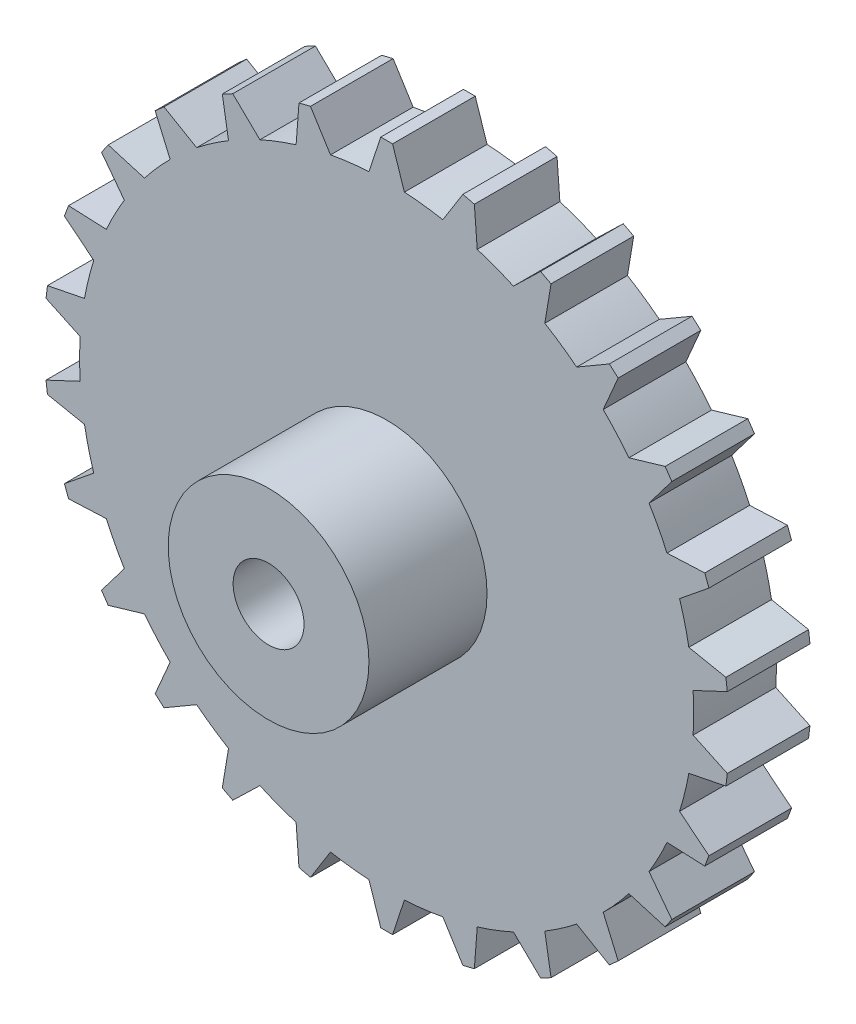
SolidWorks part; units mm, degrees
ref_plane "Front Plane" through (0, 0, 0) normal (0, 0, 1) x (1, 0, 0)
ref_plane "Top Plane" through (0, 0, 0) normal (0, 1, 0) x (1, 0, 0)
ref_plane "Right Plane" through (0, 0, 0) normal (1, 0, 0) x (0, 0, -1)
sketch "Sketch1" plane through (0, 0, 0) normal (0, 0, 1) x (1, 0, 0)
  line L0 (0, 0) -> (0, 21.7596) construction
  line L17 (6.4537, 28.2728) -> (4.7554, 25.5614)
  line L18 (6.4537, 28.2728) -> (7.4246, 28.0335)
  line L19 (7.4246, 28.0335) -> (7.6683, 24.8435)
  line L20 (13.0322, 25.9068) -> (10.7345, 23.6806)
  line L21 (13.0322, 25.9068) -> (13.9177, 25.442)
  line L22 (13.9177, 25.442) -> (13.3909, 22.2864)
  line L23 (18.8534, 22.0351) -> (16.0897, 20.4235)
  line L24 (18.8534, 22.0351) -> (19.602, 21.372)
  line L25 (19.602, 21.372) -> (18.3352, 18.4342)
  line L26 (23.579, 16.8829) -> (20.5098, 15.9796)
  line L27 (-1.5, 25.9567) -> (1.5, 25.9567) construction
  line L28 (-0.5, 28.9957) -> (0.5, 28.9957)
  line L29 (-0.5, 28.9957) -> (-1.5, 25.9567)
  line L30 (0.5, 28.9957) -> (1.5, 25.9567)
  line L31 (23.579, 16.8829) -> (24.147, 16.0599)
  line L32 (24.147, 16.0599) -> (22.214, 13.5106)
  line L33 (26.9341, 10.7495) -> (23.738, 10.6069)
  line L34 (26.9341, 10.7495) -> (27.2887, 9.8145)
  line L35 (27.2887, 9.8145) -> (24.8018, 7.8018)
  line L36 (28.724, 3.9914) -> (25.5866, 4.6178)
  line L37 (28.724, 3.9914) -> (28.8445, 2.9987)
  line L38 (28.8445, 2.9987) -> (25.9482, 1.6397)
  line L39 (28.8445, -2.9987) -> (25.9482, -1.6397)
  line L40 (28.8445, -2.9987) -> (28.724, -3.9914)
  line L41 (28.724, -3.9914) -> (25.5866, -4.6178)
  line L42 (27.2887, -9.8145) -> (24.8018, -7.8018)
  line L43 (27.2887, -9.8145) -> (26.9341, -10.7495)
  line L44 (26.9341, -10.7495) -> (23.738, -10.6069)
  line L45 (24.147, -16.0599) -> (22.214, -13.5106)
  line L46 (24.147, -16.0599) -> (23.579, -16.8829)
  line L47 (23.579, -16.8829) -> (20.5098, -15.9796)
  line L48 (19.602, -21.372) -> (18.3352, -18.4342)
  line L49 (19.602, -21.372) -> (18.8534, -22.0351)
  line L50 (18.8534, -22.0351) -> (16.0897, -20.4235)
  line L51 (13.9177, -25.442) -> (13.3909, -22.2864)
  line L52 (13.9177, -25.442) -> (13.0322, -25.9068)
  line L53 (13.0322, -25.9068) -> (10.7345, -23.6806)
  line L54 (7.4246, -28.0335) -> (7.6683, -24.8435)
  line L55 (7.4246, -28.0335) -> (6.4537, -28.2728)
  line L56 (6.4537, -28.2728) -> (4.7554, -25.5614)
  line L57 (0.5, -28.9957) -> (1.5, -25.9567)
  line L58 (0.5, -28.9957) -> (-0.5, -28.9957)
  line L59 (-0.5, -28.9957) -> (-1.5, -25.9567)
  line L60 (-6.4537, -28.2728) -> (-4.7554, -25.5614)
  line L61 (-6.4537, -28.2728) -> (-7.4246, -28.0335)
  line L62 (-7.4246, -28.0335) -> (-7.6683, -24.8435)
  line L63 (-13.0322, -25.9068) -> (-10.7345, -23.6806)
  line L64 (-13.0322, -25.9068) -> (-13.9177, -25.442)
  line L65 (-13.9177, -25.442) -> (-13.3909, -22.2864)
  line L66 (-18.8534, -22.0351) -> (-16.0897, -20.4235)
  line L67 (-18.8534, -22.0351) -> (-19.602, -21.372)
  line L68 (-19.602, -21.372) -> (-18.3352, -18.4342)
  line L69 (-23.579, -16.8829) -> (-20.5098, -15.9796)
  line L70 (-23.579, -16.8829) -> (-24.147, -16.0599)
  line L71 (-24.147, -16.0599) -> (-22.214, -13.5106)
  line L72 (-26.9341, -10.7495) -> (-23.738, -10.6069)
  line L73 (-26.9341, -10.7495) -> (-27.2887, -9.8145)
  line L74 (-27.2887, -9.8145) -> (-24.8018, -7.8018)
  line L75 (-28.724, -3.9914) -> (-25.5866, -4.6178)
  line L76 (-28.724, -3.9914) -> (-28.8445, -2.9987)
  line L77 (-28.8445, -2.9987) -> (-25.9482, -1.6397)
  line L78 (-28.8445, 2.9987) -> (-25.9482, 1.6397)
  line L79 (-28.8445, 2.9987) -> (-28.724, 3.9914)
  line L80 (-28.724, 3.9914) -> (-25.5866, 4.6178)
  line L81 (-27.2887, 9.8145) -> (-24.8018, 7.8018)
  line L82 (-27.2887, 9.8145) -> (-26.9341, 10.7495)
  line L83 (-26.9341, 10.7495) -> (-23.738, 10.6069)
  line L84 (-24.147, 16.0599) -> (-22.214, 13.5106)
  line L85 (-24.147, 16.0599) -> (-23.579, 16.8829)
  line L86 (-23.579, 16.8829) -> (-20.5098, 15.9796)
  line L87 (-19.602, 21.372) -> (-18.3352, 18.4342)
  line L88 (-19.602, 21.372) -> (-18.8534, 22.0351)
  line L89 (-18.8534, 22.0351) -> (-16.0897, 20.4235)
  line L90 (-13.9177, 25.442) -> (-13.3909, 22.2864)
  line L91 (-13.9177, 25.442) -> (-13.0322, 25.9068)
  line L92 (-13.0322, 25.9068) -> (-10.7345, 23.6806)
  line L93 (-7.4246, 28.0335) -> (-7.6683, 24.8435)
  line L94 (-7.4246, 28.0335) -> (-6.4537, 28.2728)
  line L95 (-6.4537, 28.2728) -> (-4.7554, 25.5614)
  circle A0 centre (0, 0) radius 8.5
  arc A17 (-1.5, 25.9567) -> (-4.7554, 25.5614) centre (0, 0) ccw
  arc A18 (-18.8534, 22.0351) -> (-19.602, 21.372) centre (0, 0) ccw construction
  arc A19 (4.7554, 25.5614) -> (1.5, 25.9567) centre (0, 0) ccw
  arc A20 (10.7345, 23.6806) -> (7.6683, 24.8435) centre (0, 0) ccw
  arc A21 (16.0897, 20.4235) -> (13.3909, 22.2864) centre (0, 0) ccw
  arc A22 (20.5098, 15.9796) -> (18.3352, 18.4342) centre (0, 0) ccw
  arc A23 (23.738, 10.6069) -> (22.214, 13.5106) centre (0, 0) ccw
  arc A24 (25.5866, 4.6178) -> (24.8018, 7.8018) centre (0, 0) ccw
  arc A25 (25.9482, -1.6397) -> (25.9482, 1.6397) centre (0, 0) ccw
  arc A26 (24.8018, -7.8018) -> (25.5866, -4.6178) centre (0, 0) ccw
  arc A27 (22.214, -13.5106) -> (23.738, -10.6069) centre (0, 0) ccw
  arc A28 (18.3352, -18.4342) -> (20.5098, -15.9796) centre (0, 0) ccw
  arc A29 (13.3909, -22.2864) -> (16.0897, -20.4235) centre (0, 0) ccw
  arc A30 (7.6683, -24.8435) -> (10.7345, -23.6806) centre (0, 0) ccw
  arc A31 (1.5, -25.9567) -> (4.7554, -25.5614) centre (0, 0) ccw
  arc A32 (-4.7554, -25.5614) -> (-1.5, -25.9567) centre (0, 0) ccw
  arc A33 (-10.7345, -23.6806) -> (-7.6683, -24.8435) centre (0, 0) ccw
  arc A34 (-16.0897, -20.4235) -> (-13.3909, -22.2864) centre (0, 0) ccw
  arc A35 (-20.5098, -15.9796) -> (-18.3352, -18.4342) centre (0, 0) ccw
  arc A36 (-23.738, -10.6069) -> (-22.214, -13.5106) centre (0, 0) ccw
  arc A37 (-25.5866, -4.6178) -> (-24.8018, -7.8018) centre (0, 0) ccw
  arc A38 (-25.9482, 1.6397) -> (-25.9482, -1.6397) centre (0, 0) ccw
  arc A39 (-24.8018, 7.8018) -> (-25.5866, 4.6178) centre (0, 0) ccw
  arc A40 (-22.214, 13.5106) -> (-23.738, 10.6069) centre (0, 0) ccw
  arc A41 (-18.3352, 18.4342) -> (-20.5098, 15.9796) centre (0, 0) ccw
  arc A42 (-13.3909, 22.2864) -> (-16.0897, 20.4235) centre (0, 0) ccw
  arc A43 (-7.6683, 24.8435) -> (-10.7345, 23.6806) centre (0, 0) ccw
  arc A44 (-13.0322, 25.9068) -> (-13.9177, 25.442) centre (0, 0) ccw construction
  arc A45 (-6.4537, 28.2728) -> (-7.4246, 28.0335) centre (0, 0) ccw construction
  arc A46 (7.4246, 28.0335) -> (-0.5, 28.9957) centre (0, 0) ccw construction
  arc A47 (13.9177, 25.442) -> (13.0322, 25.9068) centre (0, 0) ccw construction
  arc A48 (19.602, 21.372) -> (18.8534, 22.0351) centre (0, 0) ccw construction
  arc A49 (24.147, 16.0599) -> (23.579, 16.8829) centre (0, 0) ccw construction
  arc A50 (27.2887, 9.8145) -> (26.9341, 10.7495) centre (0, 0) ccw construction
  arc A51 (26.9341, -10.7495) -> (27.2887, -9.8145) centre (0, 0) ccw construction
  arc A52 (23.579, -16.8829) -> (24.147, -16.0599) centre (0, 0) ccw construction
  arc A53 (13.0322, -25.9068) -> (13.9177, -25.442) centre (0, 0) ccw construction
  arc A54 (18.8534, -22.0351) -> (19.602, -21.372) centre (0, 0) ccw construction
  arc A55 (-0.5, -28.9957) -> (0.5, -28.9957) centre (0, 0) ccw construction
  arc A56 (6.4537, -28.2728) -> (7.4246, -28.0335) centre (0, 0) ccw construction
  arc A57 (-7.4246, -28.0335) -> (-6.4537, -28.2728) centre (0, 0) ccw construction
  arc A58 (-13.9177, -25.442) -> (-13.0322, -25.9068) centre (0, 0) ccw construction
  arc A59 (-19.602, -21.372) -> (-18.8534, -22.0351) centre (0, 0) ccw construction
  arc A60 (-27.2887, -9.8145) -> (-26.9341, -10.7495) centre (0, 0) ccw construction
  arc A61 (-28.8445, -2.9987) -> (-28.724, -3.9914) centre (0, 0) ccw construction
  arc A62 (-28.724, 3.9914) -> (-28.8445, 2.9987) centre (0, 0) ccw construction
  arc A63 (-26.9341, 10.7495) -> (-27.2887, 9.8145) centre (0, 0) ccw construction
  arc A64 (-23.579, 16.8829) -> (-24.147, 16.0599) centre (0, 0) ccw construction
  arc A65 (-24.147, -16.0599) -> (-23.579, -16.8829) centre (0, 0) ccw construction
  arc A66 (28.8445, 2.9987) -> (28.724, 3.9914) centre (0, 0) ccw construction
  arc A67 (28.724, -3.9914) -> (28.8445, -2.9987) centre (0, 0) ccw construction
  point P41 (0, 0)
  point P112 (0, 0)
  dimension "D1" = 17
  dimension "D2" = 58
  dimension "D3" = 3
  dimension "D6" = 52
  dimension "D4" = 1.5
  dimension "D5" = 1.5
  dimension "D7" = 1
  dimension "D8" = 26
extrude "Boss-Extrude1" add sketch "Sketch1" along normal blind 7
sketch "Sketch2" plane through (0, 0, 7) normal (0, 0, 1) x (1, 0, 0)
  circle A0 centre (0, 0) radius 8.5
  circle A1 centre (0, 0) radius 3
  dimension "D1" = 6
extrude "Boss-Extrude2" add sketch "Sketch2" along normal blind 10 and the other way up to surface (7 mm away) other way up to face at (8.5, 0, 0)
